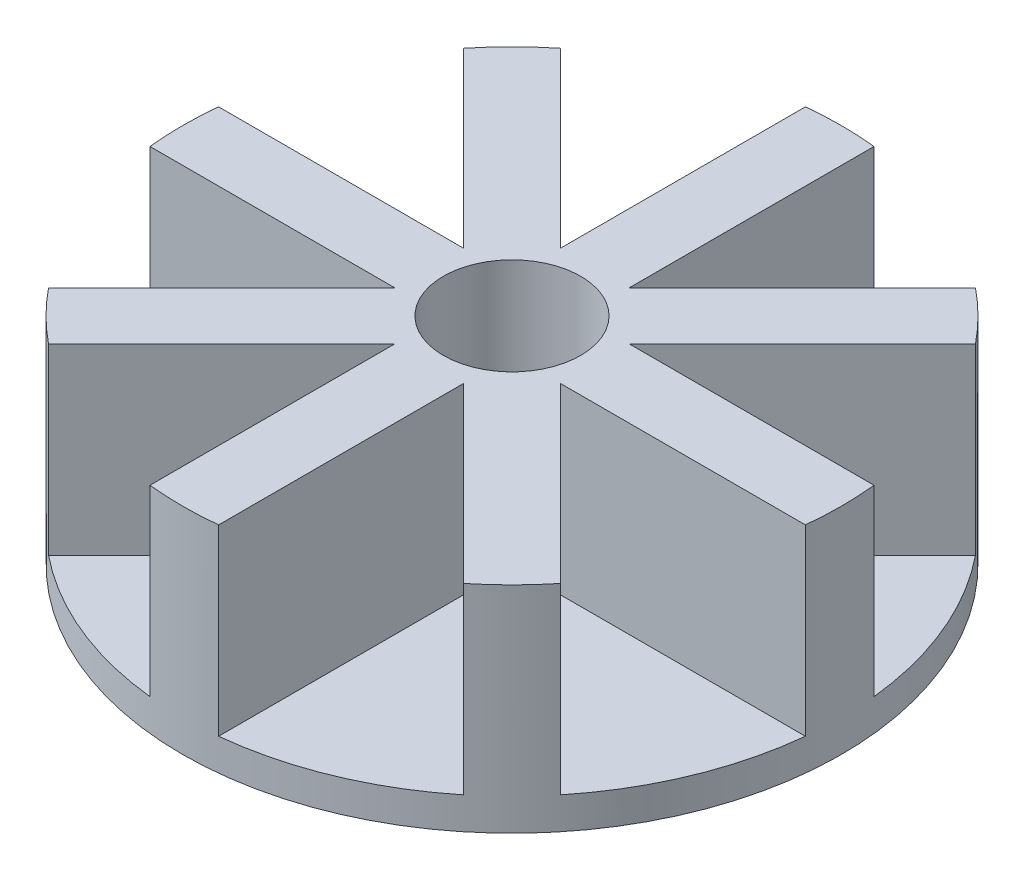
SolidWorks part; units mm, degrees
ref_plane "Front Plane" through (0, 0, 0) normal (0, 0, 1) x (1, 0, 0)
ref_plane "Top Plane" through (0, 0, 0) normal (0, 1, 0) x (1, 0, 0)
ref_plane "Right Plane" through (0, 0, 0) normal (1, 0, 0) x (0, 0, -1)
sketch "Sketch1" plane through (0, 0, 0) normal (0, 1, 0) x (1, 0, 0)
  circle A0 centre (0, 0) radius 144
  dimension "D1" = 288
extrude "Boss-Extrude1" add sketch "Sketch1" along normal blind 94
sketch "Sketch2" plane through (0, 94, 0) normal (0, 1, 0) x (1, 0, 0)
  line L0 (111.876, 90.6628) -> (32.9673, 11.7541)
  line L2 (-15, 143.2166) -> (-15, 31.6228)
  line L4 (15, 143.2166) -> (15, 31.6228)
  line L5 (90.6628, 111.876) -> (11.7541, 32.9673)
  line L6 (143.2166, -15) -> (31.6228, -15)
  line L7 (143.2166, 15) -> (31.6228, 15)
  line L8 (90.6628, -111.876) -> (11.7541, -32.9673)
  line L9 (111.876, -90.6628) -> (32.9673, -11.7541)
  line L10 (-15, -143.2166) -> (-15, -31.6228)
  line L11 (15, -143.2166) -> (15, -31.6228)
  line L12 (-111.876, -90.6628) -> (-32.9673, -11.7541)
  line L13 (-90.6628, -111.876) -> (-11.7541, -32.9673)
  line L14 (-143.2166, 15) -> (-31.6228, 15)
  line L15 (-143.2166, -15) -> (-31.6228, -15)
  line L16 (-90.6628, 111.876) -> (-11.7541, 32.9673)
  line L17 (-111.876, 90.6628) -> (-32.9673, 11.7541)
  circle A0 centre (0, 0) radius 35
  arc A1 (-15, 143.2166) -> (15, 143.2166) centre (0, 0) cw
  circle A2 centre (0, 0) radius 144 construction
  arc A3 (-15, 31.6228) -> (15, 31.6228) centre (0, 0) cw
  arc A4 (11.7541, 32.9673) -> (32.9673, 11.7541) centre (0, 0) cw
  arc A5 (90.6628, 111.876) -> (111.876, 90.6628) centre (0, 0) cw
  arc A6 (31.6228, 15) -> (31.6228, -15) centre (0, 0) cw
  arc A7 (143.2166, 15) -> (143.2166, -15) centre (0, 0) cw
  arc A8 (32.9673, -11.7541) -> (11.7541, -32.9673) centre (0, 0) cw
  arc A9 (111.876, -90.6628) -> (90.6628, -111.876) centre (0, 0) cw
  arc A10 (15, -31.6228) -> (-15, -31.6228) centre (0, 0) cw
  arc A11 (15, -143.2166) -> (-15, -143.2166) centre (0, 0) cw
  arc A12 (-11.7541, -32.9673) -> (-32.9673, -11.7541) centre (0, 0) cw
  arc A13 (-90.6628, -111.876) -> (-111.876, -90.6628) centre (0, 0) cw
  arc A14 (-31.6228, -15) -> (-31.6228, 15) centre (0, 0) cw
  arc A15 (-143.2166, -15) -> (-143.2166, 15) centre (0, 0) cw
  arc A16 (-32.9673, 11.7541) -> (-11.7541, 32.9673) centre (0, 0) cw
  arc A17 (-111.876, 90.6628) -> (-90.6628, 111.876) centre (0, 0) cw
  point P3 (0, 86.5524)
  circle M8 centre (0, 0) radius 144
  dimension "D1" = 70
  dimension "D2" = 30
  dimension "D3" = 15
  dimension "D4" = 8
extrude "Cut-Extrude1" cut sketch "Sketch2" against normal blind 80 contours L16 L2 M8 | L5 L4 M8 | L7 L0 M8 | L9 L6 M8 | L11 L8 M8 | L13 L10 M8 | L15 L12 M8 | L17 L14 M8
sketch "Sketch3" plane through (0, 0, 0) normal (0, -1, 0) x (1, 0, 0)
  circle A0 centre (0, 0) radius 4
  dimension "D1" = 8
extrude "Cut-Extrude2" cut sketch "Sketch3" against normal blind 20
sketch "Sketch4" plane through (0, 0, 0) normal (0, -1, 0) x (1, 0, 0)
  line L1 (-15.5, 15.5) -> (15.5, 15.5) construction
  line L2 (-15.5, 15.5) -> (-15.5, -15.5) construction
  line L3 (-15.5, -15.5) -> (15.5, -15.5) construction
  line L4 (15.5, 15.5) -> (15.5, -15.5) construction
  line L5 (-15.5, 15.5) -> (15.5, -15.5) construction
  line L6 (-15.5, -15.5) -> (15.5, 15.5) construction
  circle A0 centre (15.5, -15.5) radius 1.4
  circle A1 centre (15.5, 15.5) radius 1.4
  circle A2 centre (-15.5, 15.5) radius 1.4
  circle A3 centre (-15.5, -15.5) radius 1.4
  point P0 (0, 0)
  dimension "D3" = 2.8
  dimension "D1" = 31
  dimension "D2" = 31
extrude "Cut-Extrude3" cut sketch "Sketch4" against normal up to next
sketch "Sketch5" plane through (0, 94, 0) normal (0, 1, 0) x (1, 0, 0)
  circle A0 centre (0, 0) radius 30
  dimension "D1" = 60
extrude "Cut-Extrude4" cut sketch "Sketch5" against normal up to surface (80 mm away) up to face at (-40.9793, 14, 98.9327)
